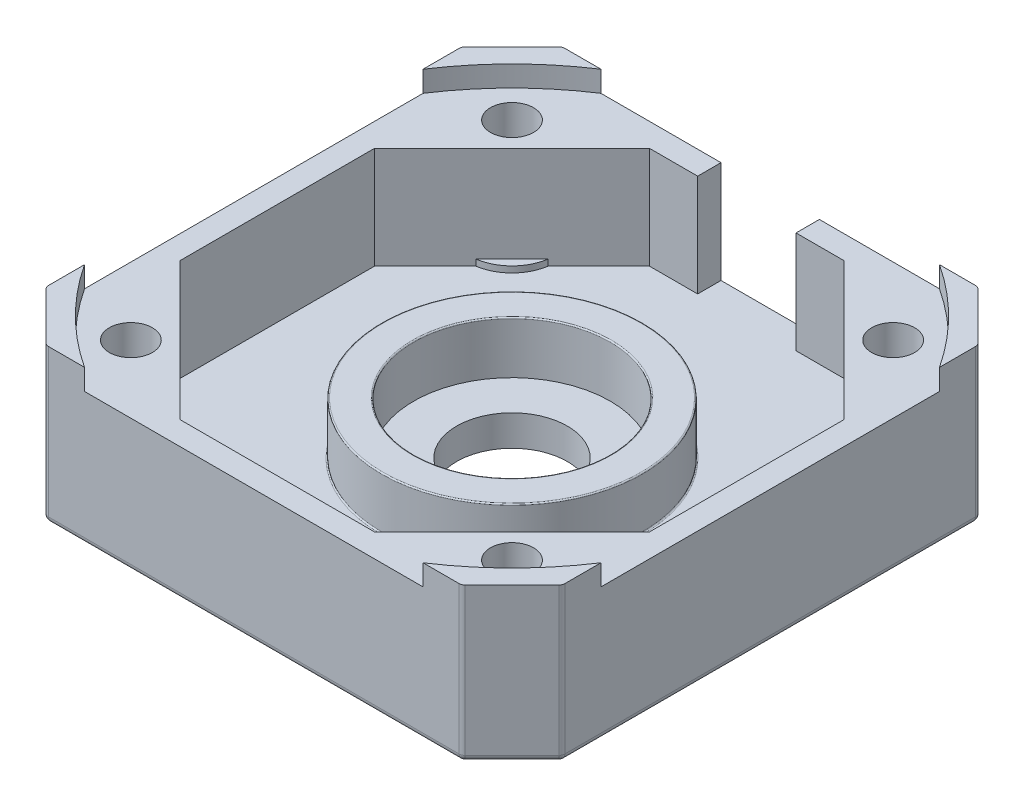
SolidWorks part; units mm, degrees
material "Д16Т ГОСТ 4784-97"
ref_plane "Спереди" through (0, 0, 0) normal (0, 0, 1) x (1, 0, 0)
ref_plane "Сверху" through (0, 0, 0) normal (0, 1, 0) x (1, 0, 0)
ref_plane "Справа" through (0, 0, 0) normal (1, 0, 0) x (0, 0, -1)
sketch "Эскиз1" plane through (0, 0, 0) normal (0, 1, 0) x (1, 0, 0)
  line L1 (-21, 21) -> (21, 21)
  line L2 (-21, 21) -> (-21, -21)
  line L3 (-21, -21) -> (21, -21)
  line L4 (21, 21) -> (21, -21)
  line L5 (-21, 21) -> (21, -21) construction
  line L6 (-21, -21) -> (21, 21) construction
  point P0 (0, 0)
  dimension "D1" = 42
extrude "Бобышка-Вытянуть1" add sketch "Эскиз1" along normal blind 12.5
sketch "Эскиз2" plane through (0, 12.5, 0) normal (0, 1, 0) x (1, 0, 0)
  line L0 (-21, 21) -> (-21, 16.9009)
  line L1 (-21, 21) -> (-21, -21) construction
  line L2 (-21, 16.9009) -> (-16.9009, 21)
  line L3 (21, 21) -> (-21, 21) construction
  line L4 (-16.9009, 21) -> (-21, 21)
  line L5 (21, 21) -> (16.9009, 21)
  line L6 (16.9009, 21) -> (21, 16.9009)
  line L7 (21, -21) -> (21, 21) construction
  line L8 (21, 16.9009) -> (21, 21)
  line L9 (-21, -21) -> (-21, -16.9009)
  line L10 (-21, -16.9009) -> (-16.9009, -21)
  line L11 (-21, -21) -> (21, -21) construction
  line L12 (-16.9009, -21) -> (-21, -21)
  line L13 (21, -21) -> (21, -16.9009)
  line L14 (21, -16.9009) -> (16.9009, -21)
  line L15 (16.9009, -21) -> (21, -21)
  dimension "D1" = 53.6
extrude "Вырез-Вытянуть1" cut sketch "Эскиз2" against normal up to surface (12.5 mm away) up to face at (0, 0, 0)
sketch "Эскиз3" plane through (0, 12.5, 0) normal (0, 1, 0) x (1, 0, 0)
  line L0 (-7.9115, 19.1) -> (7.9115, 19.1)
  line L1 (7.9115, 19.1) -> (19.1, 7.9115)
  line L2 (19.1, 7.9115) -> (19.1, -7.9115)
  line L3 (19.1, -7.9115) -> (7.9115, -19.1)
  line L4 (7.9115, -19.1) -> (-7.9115, -19.1)
  line L5 (-7.9115, -19.1) -> (-19.1, -7.9115)
  line L6 (-19.1, -7.9115) -> (-19.1, 7.9115)
  line L7 (-19.1, 7.9115) -> (-7.9115, 19.1)
  line L8 (-21, 16.9009) -> (-16.9009, 21) construction
  line L9 (16.9009, 21) -> (21, 16.9009) construction
  line L10 (21, -16.9009) -> (16.9009, -21) construction
  line L11 (-16.9009, -21) -> (-21, -16.9009) construction
  line L12 (-19.1, 0) -> (0, 0) construction
  line L13 (0, 0) -> (19.1, 0) construction
  line L14 (0, 19.1) -> (0, 0) construction
  line L15 (0, 0) -> (0, -19.1) construction
  dimension "D1" = 38.2
  dimension "D2" = 38.2
extrude "Вырез-Вытянуть2" cut sketch "Эскиз3" against normal blind 10
sketch "Эскиз4" plane through (0, 12.5, 0) normal (0, 1, 0) x (1, 0, 0)
  circle A0 centre (0, 0) radius 25.11
  dimension "D1" = 50.22
extrude "Вырез-Вытянуть3" cut sketch "Эскиз4" against normal blind 1.7
sketch "Эскиз5" plane through (0, 2.5, 0) normal (0, 1, 0) x (1, 0, 0)
  circle A0 centre (0, 0) radius 10.6
  circle A1 centre (0, 0) radius 8
  dimension "D1" = 21.2
  dimension "D2" = 16
extrude "Бобышка-Вытянуть2" add sketch "Эскиз5" along normal blind 4.25
sketch "Эскиз6" plane through (0, 2.5, 0) normal (0, 1, 0) x (1, 0, 0)
  circle A0 centre (0, 0) radius 4.5
  dimension "D1" = 9
extrude "Вырез-Вытянуть4" cut sketch "Эскиз6" against normal up to surface (2.5 mm away) up to face at (0, 0, 0)
sketch "Эскиз8" plane through (0, 10.8, 0) normal (0, 1, 0) x (1, 0, 0)
  line L1 (15.5, -15.5) -> (-15.5, -15.5) construction
  line L2 (15.5, -15.5) -> (15.5, 15.5) construction
  line L3 (15.5, 15.5) -> (-15.5, 15.5) construction
  line L4 (-15.5, -15.5) -> (-15.5, 15.5) construction
  line L5 (15.5, -15.5) -> (-15.5, 15.5) construction
  line L6 (15.5, 15.5) -> (-15.5, -15.5) construction
  circle A0 centre (-15.5, 15.5) radius 1.75
  circle A1 centre (15.5, 15.5) radius 1.75
  circle A2 centre (-15.5, -15.5) radius 1.75
  circle A3 centre (15.5, -15.5) radius 1.75
  point P0 (0, 0)
  dimension "D2" = 3.5
  dimension "D1" = 31
extrude "Вырез-Вытянуть5" cut sketch "Эскиз8" against normal up to surface (10.8 mm away) up to face at (0, 0, 4.5)
sketch "Эскиз9" plane through (0, 0, 0) normal (0, -1, 0) x (1, 0, 0)
  circle A0 centre (-15.5, 15.5) radius 3
  circle A1 centre (15.5, 15.5) radius 3
  circle A2 centre (15.5, -15.5) radius 3
  circle A3 centre (-15.5, -15.5) radius 3
  dimension "D1" = 6
extrude "Вырез-Вытянуть6" cut sketch "Эскиз9" against normal blind 2.62
sketch "Эскиз11" plane through (0, 2.5, 0) normal (0, 1, 0) x (1, 0, 0)
  line L0 (19.1, -7.9115) -> (7.9115, -19.1) construction
  line L1 (-7.9115, -19.1) -> (-19.1, -7.9115) construction
  line L2 (-19.1, 7.9115) -> (-7.9115, 19.1) construction
  line L3 (7.9115, 19.1) -> (19.1, 7.9115) construction
  line L4 (14.9713, -12.0402) -> (12.0402, -14.9713)
  line L5 (-12.0402, -14.9713) -> (-14.9713, -12.0402)
  line L6 (-14.9713, 12.0402) -> (-12.0402, 14.9713)
  line L7 (12.0402, 14.9713) -> (14.9713, 12.0402)
  arc A0 (-14.9713, 12.0402) -> (-12.0402, 14.9713) centre (-15.5, 15.5) ccw
  arc A1 (12.0402, 14.9713) -> (14.9713, 12.0402) centre (15.5, 15.5) ccw
  arc A2 (-12.0402, -14.9713) -> (-14.9713, -12.0402) centre (-15.5, -15.5) ccw
  arc A3 (14.9713, -12.0402) -> (12.0402, -14.9713) centre (15.5, -15.5) ccw
  arc A4 (-14.2289, 12.7826) -> (-12.7826, 14.2289) centre (-15.5, 15.5) ccw construction
  dimension "D1" = 0.5
extrude "Бобышка-Вытянуть3" add sketch "Эскиз11" along normal blind 0.5
sketch "Эскиз12" plane through (0, 2.5, 0) normal (0, -1, 0) x (1, 0, 0)
  line L1 (-14.2289, -12.7826) -> (-12.7826, -14.2289)
  line L2 (-14.2289, -12.7826) -> (-12.7826, -14.2289)
  line L3 (-12.7826, 14.2289) -> (-14.2289, 12.7826)
  line L4 (-12.7826, 14.2289) -> (-14.2289, 12.7826)
  line L5 (14.2289, 12.7826) -> (12.7826, 14.2289)
  line L6 (14.2289, 12.7826) -> (12.7826, 14.2289)
  line L7 (12.7826, -14.2289) -> (14.2289, -12.7826)
  line L8 (12.7826, -14.2289) -> (14.2289, -12.7826)
  arc A1 (-12.7826, -14.2289) -> (-14.2289, -12.7826) centre (-15.5, -15.5) ccw
  arc A2 (-12.7826, -14.2289) -> (-14.2289, -12.7826) centre (-15.5, -15.5) ccw
  arc A3 (-14.2289, 12.7826) -> (-12.7826, 14.2289) centre (-15.5, 15.5) ccw
  arc A4 (-14.2289, 12.7826) -> (-12.7826, 14.2289) centre (-15.5, 15.5) ccw
  arc A5 (12.7826, 14.2289) -> (14.2289, 12.7826) centre (15.5, 15.5) ccw
  arc A6 (12.7826, 14.2289) -> (14.2289, 12.7826) centre (15.5, 15.5) ccw
  arc A7 (14.2289, -12.7826) -> (12.7826, -14.2289) centre (15.5, -15.5) ccw
  arc A8 (14.2289, -12.7826) -> (12.7826, -14.2289) centre (15.5, -15.5) ccw
  dimension "D1" = 0
  dimension "D2" = 0
  dimension "D3" = 0
  dimension "D4" = 0
extrude "Вырез-Вытянуть7" cut sketch "Эскиз12" against normal up to surface (0.12 mm away) up to face at (15.5, 2.62, -17.25)
sketch "Эскиз13" plane through (0, 0, -21) normal (0, 0, -1) x (-1, 0, 0)
  line L0 (-16.9009, 0) -> (16.9009, 0) construction
  line L1 (-4, 10.8) -> (4, 10.8)
  line L2 (-4, 10.8) -> (-4, 2.5)
  line L3 (-4, 2.5) -> (4, 2.5)
  line L4 (4, 10.8) -> (4, 2.5)
  line L5 (-4, 10.8) -> (4, 2.5) construction
  line L6 (-4, 2.5) -> (4, 10.8) construction
  line L7 (-13.7663, 10.8) -> (13.7663, 10.8) construction
  point P0 (0, 6.65)
  dimension "D1" = 2.5
  dimension "D2" = 8
extrude "Вырез-Вытянуть8" cut sketch "Эскиз13" against normal up to surface (1.9 mm away) up to face at (0, 6.65, -19.1)
fillet "Скругление1" radius 0.1 7 edges at (0, 6.75, 8) (0, 6.75, 10.6) (0, 2.5, -10.6) (-15.5, 0, 12.5) (-15.5, 0, -18.5) (15.5, 0, -18.5) (15.5, 0, 12.5)
fillet "Скругление2" radius 0.5 16 edges at (-16.9009, 6.25, -21) (-21, 6.25, -16.9009) (16.9009, 6.25, -21) (21, 6.25, -16.9009) (18.9505, 0, -18.9505) (0, 0, -21) (-18.9505, 0, -18.9505) (-21, 0, 0) (18.9505, 0, 18.9505) (21, 0, 0) (21, 6.25, 16.9009) (16.9009, 6.25, 21) (-21, 6.25, 16.9009) (-16.9009, 6.25, 21) (-18.9505, 0, 18.9505) (0, 0, 21)
